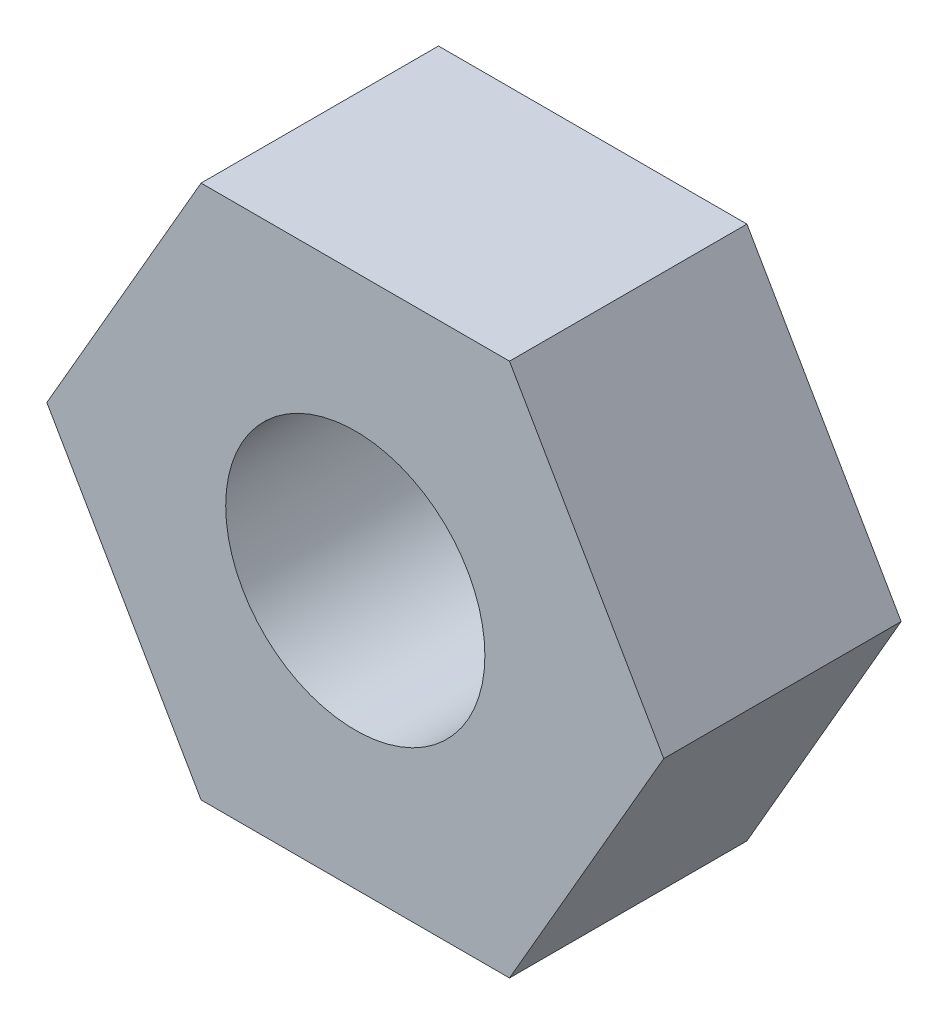
SolidWorks part; units mm, degrees
ref_plane "Front Plane" through (0, 0, 0) normal (0, 0, 1) x (1, 0, 0)
ref_plane "Top Plane" through (0, 0, 0) normal (0, 1, 0) x (1, 0, 0)
ref_plane "Right Plane" through (0, 0, 0) normal (1, 0, 0) x (0, 0, -1)
sketch "Sketch1" plane through (0, 0, 0) normal (0, 0, 1) x (1, 0, 0)
  line L0 (55, 0) -> (-55, 0) construction
  line L1 (3.9595, 0) -> (1.9797, 3.429)
  line L2 (1.9797, 3.429) -> (-1.9797, 3.429)
  line L3 (-1.9797, 3.429) -> (-3.9595, 0)
  line L4 (-3.9595, 0) -> (-1.9797, -3.429)
  line L5 (-1.9797, -3.429) -> (1.9797, -3.429)
  line L6 (1.9797, -3.429) -> (3.9595, 0)
  circle A0 centre (0, 0) radius 3.429 construction
  circle A1 centre (0, 0) radius 1.6637
  dimension "D2" = 3.3274
  dimension "D1" = 6.858
extrude "Boss-Extrude1" add sketch "Sketch1" along normal blind 3.048
